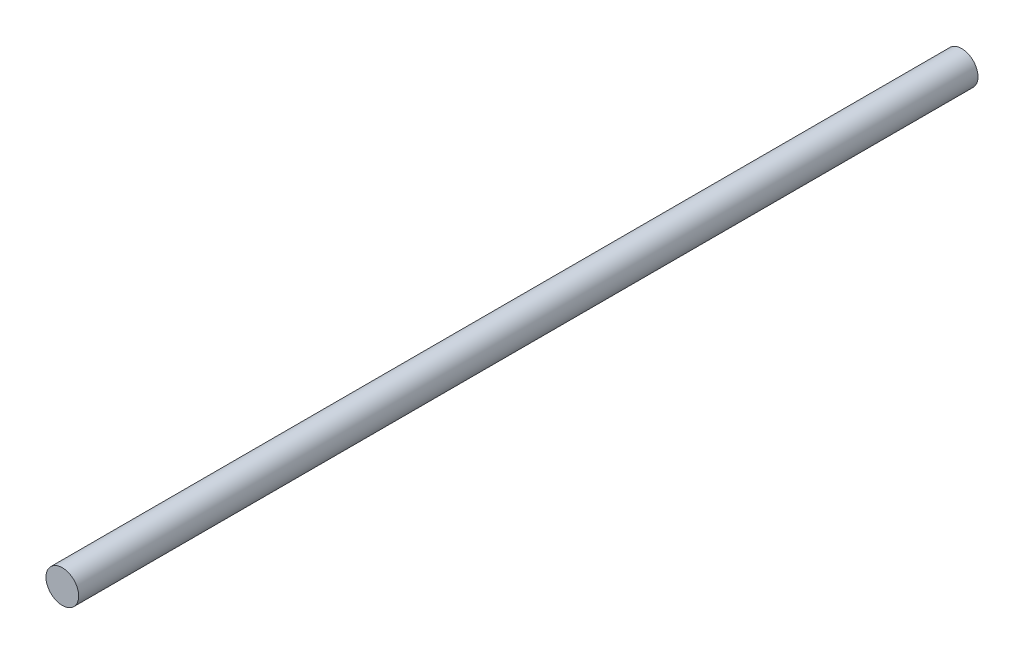
SolidWorks part; units mm, degrees
material "1.4000 (X6Cr13)"
ref_plane "Plano frontal" through (0, 0, 0) normal (0, 0, 1) x (1, 0, 0)
ref_plane "Plano superior" through (0, 0, 0) normal (0, 1, 0) x (1, 0, 0)
ref_plane "Plano direito" through (0, 0, 0) normal (1, 0, 0) x (0, 0, -1)
sketch "Esboço1" plane through (0, 0, 0) normal (0, 0, 1) x (1, 0, 0)
  circle A0 centre (0, 0) radius 4
extrude "Ressalto-extrusão1" add sketch "Esboço1" along normal blind 220
